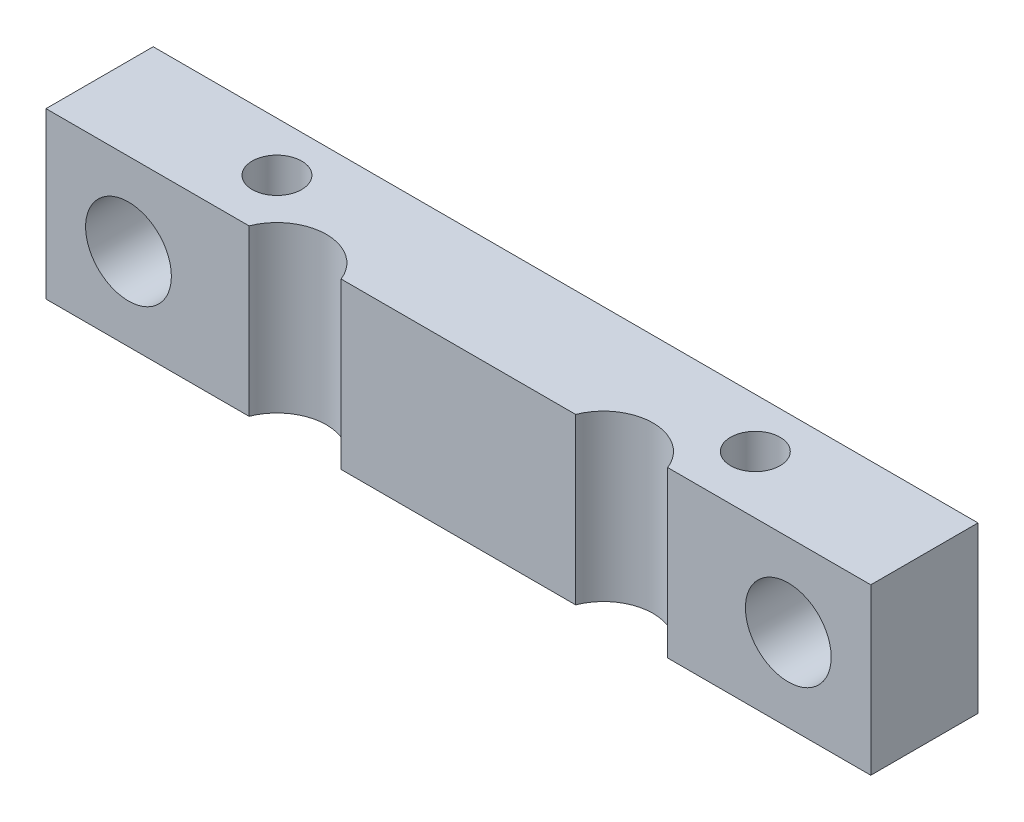
SolidWorks part; units mm, degrees
material "ABS"
ref_plane "Front Plane" through (0, 0, 0) normal (0, 0, 1) x (1, 0, 0)
ref_plane "Top Plane" through (0, 0, 0) normal (0, 1, 0) x (1, 0, 0)
ref_plane "Right Plane" through (0, 0, 0) normal (1, 0, 0) x (0, 0, -1)
sketch "Sketch1" plane through (0, 0, 0) normal (0, 1, 0) x (1, 0, 0)
  line L0 (0, 0) -> (12.3096, 0)
  line L1 (50, 0) -> (50, 6.5)
  line L2 (50, 6.5) -> (0, 6.5)
  line L3 (0, 6.5) -> (0, 0)
  line L4 (15.1005, -1.1005) -> (34.8995, -1.1005) construction
  line L5 (15.1005, -1.1005) -> (15.1005, -20.8995) construction
  line L6 (10.5, 3.5) -> (0, 3.5) construction
  line L7 (39.5, 3.5) -> (50, 3.5) construction
  line L8 (17.8914, 0) -> (32.1086, 0)
  line L9 (37.6904, 0) -> (50, 0)
  circle A0 centre (10.5, 3.5) radius 1.5
  circle A1 centre (39.5, 3.5) radius 1.5
  circle A2 centre (25, -11) radius 17.5 construction
  circle A3 centre (25, -11) radius 14 construction
  arc A5 (37.6904, 0) -> (32.1086, 0) centre (34.8995, -1.1005) ccw
  arc A7 (17.8914, 0) -> (12.3096, 0) centre (15.1005, -1.1005) ccw
  dimension "D3" = 3
  dimension "D4" = 3
  dimension "D6" = 3
  dimension "D7" = 35
  dimension "D8" = 25
  dimension "D9" = 28
  dimension "D11" = 29
  dimension "D1" = 50
  dimension "D2" = 6.5
extrude "Boss-Extrude1" add sketch "Sketch1" along normal blind 10
sketch "Sketch2" plane through (0, 0, 0) normal (0, 0, 1) x (1, 0, 0)
  line L0 (5, 5) -> (0, 5) construction
  line L1 (0, 10) -> (0, 0) construction
  line L2 (45, 5) -> (50, 5) construction
  line L3 (50, 10) -> (50, 0) construction
  circle A0 centre (5, 5) radius 2.6
  circle A1 centre (45, 5) radius 2.6
  dimension "D1" = 5.2
  dimension "D2" = 5
extrude "Cut-Extrude1" cut sketch "Sketch2" against normal up to next
equation "\"D8@Sketch1\"=\"D1@Sketch1\"/2"
